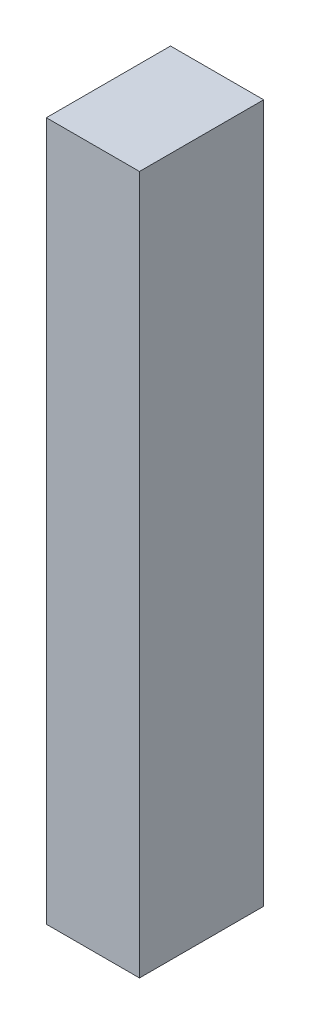
SolidWorks part; units mm, degrees
ref_plane "Front Plane" through (0, 0, 0) normal (0, 0, 1) x (1, 0, 0)
ref_plane "Top Plane" through (0, 0, 0) normal (0, 1, 0) x (1, 0, 0)
ref_plane "Right Plane" through (0, 0, 0) normal (1, 0, 0) x (0, 0, -1)
sketch "Sketch1" plane through (0, 0, 0) normal (0, 1, 0) x (1, 0, 0)
  line L1 (-3, 4) -> (3, 4)
  line L2 (-3, 4) -> (-3, -4)
  line L3 (-3, -4) -> (3, -4)
  line L4 (3, 4) -> (3, -4)
  line L5 (0, -4) -> (0, 4) construction
  line L6 (-3, 0) -> (3, 0) construction
  point P0 (0, 0)
  dimension "D1" = 8
  dimension "D2" = 6
extrude "Boss-Extrude1" add sketch "Sketch1" along normal blind 45
